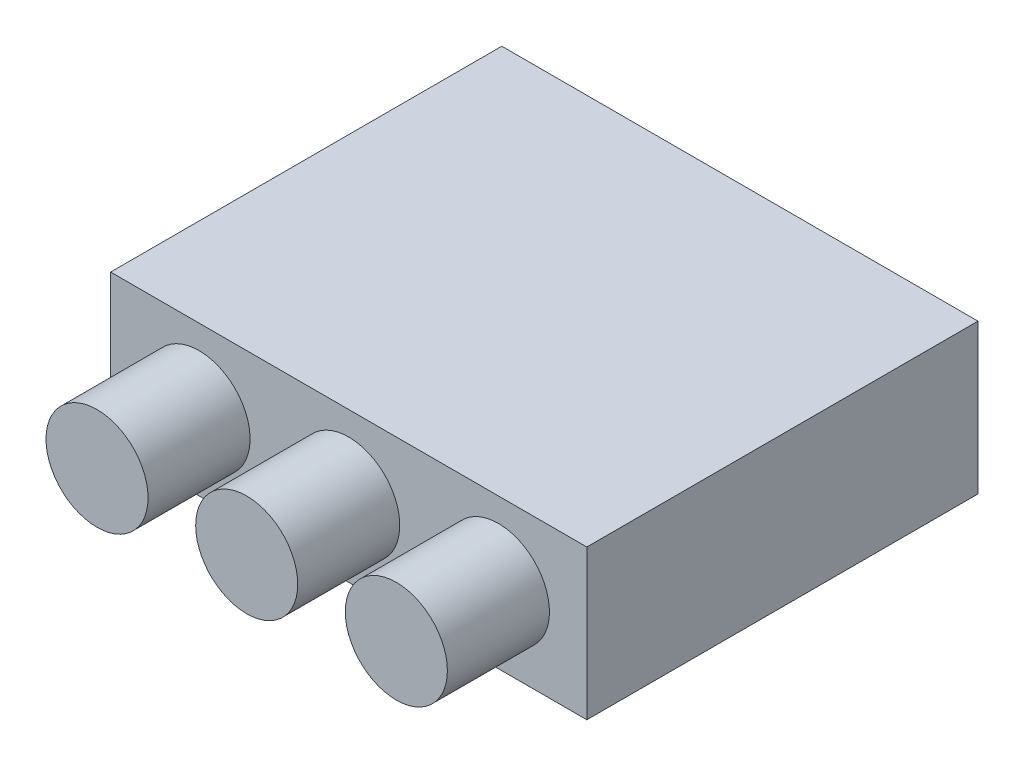
SolidWorks part; units mm, degrees
ref_plane "前视基准面" through (0, 0, 0) normal (0, 0, 1) x (1, 0, 0)
ref_plane "上视基准面" through (0, 0, 0) normal (0, 1, 0) x (1, 0, 0)
ref_plane "右视基准面" through (0, 0, 0) normal (1, 0, 0) x (0, 0, -1)
sketch "草图1" plane through (0, 0, 0) normal (0, 1, 0) x (1, 0, 0)
  line L1 (-35, 28.75) -> (35, 28.75)
  line L2 (-35, 28.75) -> (-35, -28.75)
  line L3 (-35, -28.75) -> (35, -28.75)
  line L4 (35, 28.75) -> (35, -28.75)
  line L5 (-35, 28.75) -> (35, -28.75) construction
  line L6 (-35, -28.75) -> (35, 28.75) construction
  point P0 (0, 0)
  dimension "D1" = 70
  dimension "D2" = 57.5
extrude "凸台-拉伸1" add sketch "草图1" along normal blind 22
sketch "草图2" plane through (0, 0, 28.75) normal (0, 0, 1) x (1, 0, 0)
  line L0 (-35, 22) -> (-35, 0) construction
  circle A0 centre (-22, 11) radius 7.5
  circle A1 centre (0, 11) radius 7.5
  circle A2 centre (22, 11) radius 7.5
  point P8 (-35, 11)
  dimension "D1" = 15
  dimension "D2" = 15
  dimension "D3" = 15
  dimension "D5" = 22
  dimension "D4" = 22
extrude "凸台-拉伸2" add sketch "草图2" along normal blind 15
sketch "草图3" plane through (0, 0, 0) normal (0, -1, 0) x (1, 0, 0)
  line L0 (-32, 25) -> (-32, -25) construction
  line L1 (-32, -25) -> (32, -25) construction
  circle A0 centre (-32, 25) radius 1
  circle A1 centre (-32, -25) radius 1
  circle A2 centre (32, -25) radius 1
  circle A3 centre (32, 25) radius 1
  point P8 (0, -25)
  point P9 (-32, 0)
  point P10 (0, 0)
  dimension "D1" = 2
  dimension "D2" = 2
  dimension "D3" = 2
  dimension "D4" = 2
  dimension "D6" = 50
  dimension "D7" = 64
  dimension "D5" = 64
extrude "切除-拉伸1" cut sketch "草图3" against normal blind 5
